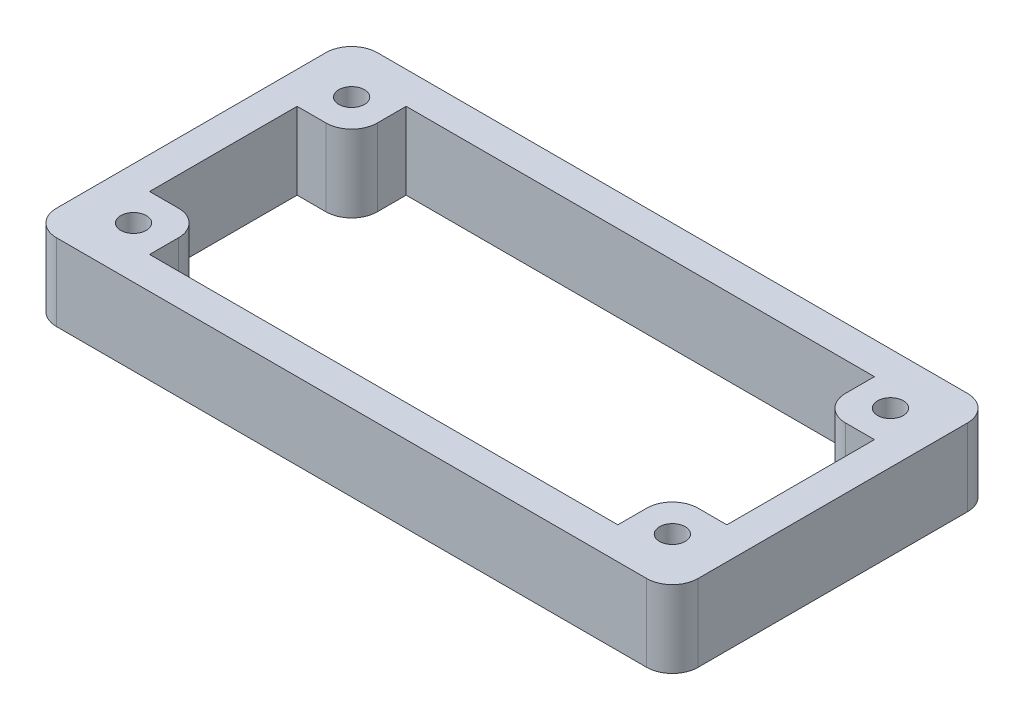
SolidWorks part; units mm, degrees
ref_plane "Front Plane" through (0, 0, 0) normal (0, 0, 1) x (1, 0, 0)
ref_plane "Top Plane" through (0, 0, 0) normal (0, 1, 0) x (1, 0, 0)
ref_plane "Right Plane" through (0, 0, 0) normal (1, 0, 0) x (0, 0, -1)
sketch "Sketch1" plane through (0, 0, 0) normal (0, 1, 0) x (1, 0, 0)
  line L1 (-25, 12.5) -> (25, 12.5)
  line L2 (-25, 12.5) -> (-25, -12.5)
  line L3 (-25, -12.5) -> (25, -12.5)
  line L4 (25, 12.5) -> (25, -12.5)
  line L5 (-25, 12.5) -> (25, -12.5) construction
  line L6 (-25, -12.5) -> (25, 12.5) construction
  point P0 (0, 0)
  dimension "D1" = 50
  dimension "D2" = 25
extrude "Boss-Extrude1" add sketch "Sketch1" along normal blind 6
sketch "Sketch2" plane through (0, 0, 0) normal (0, 1, 0) x (1, 0, 0)
  line L0 (-21, 8.5) -> (21, 8.5) construction
  line L1 (21, 8.5) -> (21, -8.5) construction
  line L2 (21, -8.5) -> (-21, -8.5) construction
  line L3 (-21, -8.5) -> (-21, 8.5) construction
  circle A0 centre (-21, 8.5) radius 1
  circle A1 centre (21, 8.5) radius 0.9998
  circle A2 centre (-21, -8.5) radius 1
  circle A3 centre (21, -8.5) radius 1
  dimension "D2" = 1.9996
  dimension "D3" = 2
  dimension "D4" = 2
  dimension "D5" = 2
  dimension "D1" = 42
  dimension "D6" = 21
  dimension "D7" = 17
  dimension "D8" = 8.5
extrude "Cut-Extrude1" cut sketch "Sketch2" along normal blind 6
sketch "Sketch3" plane through (0, 0, 0) normal (0, 1, 0) x (1, 0, 0)
  line L0 (-22.5, 5.75) -> (-22.5, -5.75)
  line L2 (-18.25, -10) -> (18.25, -10)
  line L4 (22.5, -5.75) -> (22.5, 5.75)
  line L6 (18.25, 10) -> (-18.25, 10)
  line L8 (-22.5, 5.75) -> (-18.25, 5.75)
  line L9 (-18.25, 5.75) -> (-18.25, 10)
  line L10 (-22.5, -5.75) -> (-18.25, -5.75)
  line L11 (-18.25, -5.75) -> (-18.25, -10)
  line L12 (18.25, -10) -> (18.25, -5.75)
  line L13 (18.25, -5.75) -> (22.5, -5.75)
  line L14 (22.5, 5.75) -> (18.25, 5.75)
  line L15 (18.25, 5.75) -> (18.25, 10)
  point P2 (-20.375, 5.75)
  dimension "D8" = 36.5
  dimension "D1" = 45
  dimension "D2" = 20
  dimension "D3" = 10
  dimension "D4" = 22.5
  dimension "D5" = 5.75
  dimension "D6" = 11.5
  dimension "D7" = 18.25
  dimension "D9" = 5.75
  dimension "D10" = 11.5
  dimension "D11" = 36.5
  dimension "D12" = 18.25
extrude "Cut-Extrude2" cut sketch "Sketch3" along normal blind 6
fillet "Fillet1" radius 2 8 edges at (-25, 3, 12.5) (25, 3, 12.5) (25, 3, -12.5) (-25, 3, -12.5) (18.25, 3, 5.75) (18.25, 3, -5.75) (-18.25, 3, 5.75) (-18.25, 3, -5.75)
